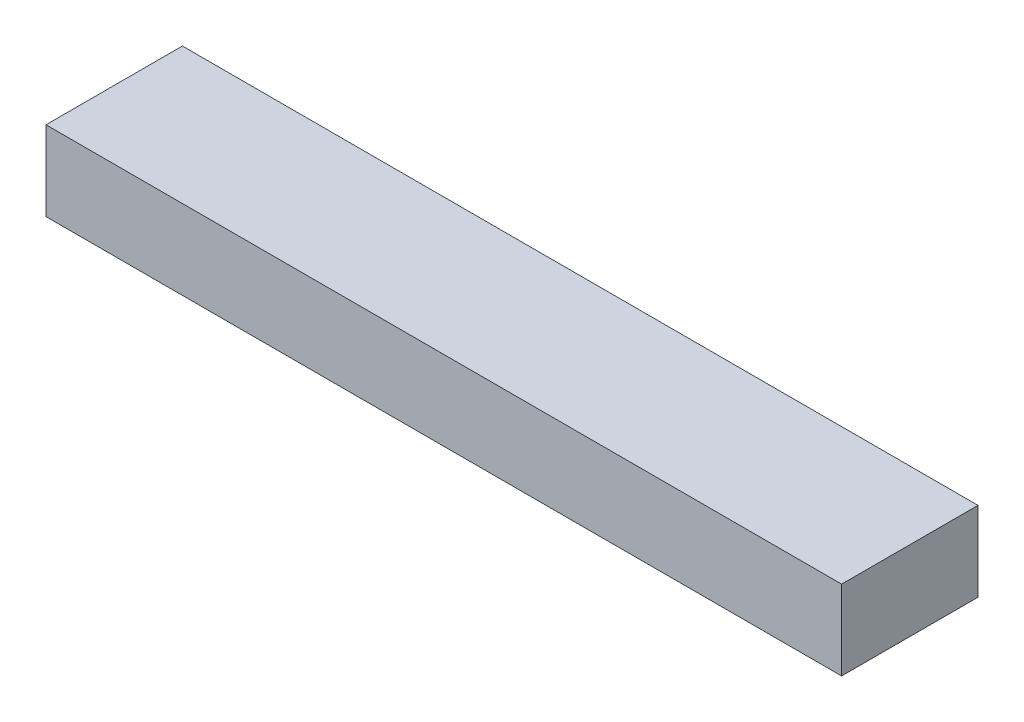
SolidWorks part; units mm, degrees
ref_plane "Face" through (0, 0, 0) normal (0, 0, 1) x (1, 0, 0)
ref_plane "Dessus" through (0, 0, 0) normal (0, 1, 0) x (1, 0, 0)
ref_plane "Droite" through (0, 0, 0) normal (1, 0, 0) x (0, 0, -1)
sketch "Esquisse1" plane through (0, 0, 0) normal (0, 1, 0) x (1, 0, 0)
  line L1 (0, 0) -> (700, 0)
  line L2 (0, 0) -> (0, 120)
  line L3 (0, 120) -> (700, 120)
  line L4 (700, 0) -> (700, 120)
  dimension "D1" = 700
  dimension "D2" = 120
extrude "Extrusion1" add sketch "Esquisse1" along normal blind 70
